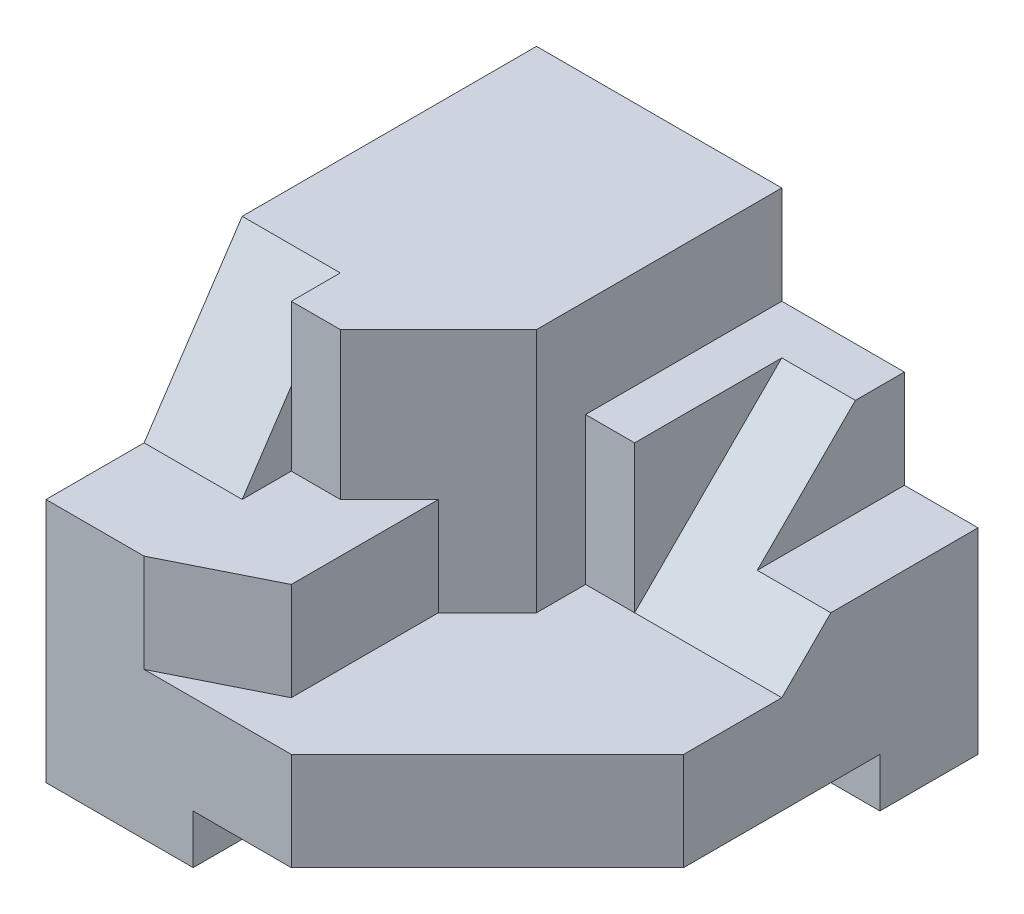
SolidWorks part; units mm, degrees
ref_plane "Front Plane" through (0, 0, 0) normal (0, 0, 1) x (1, 0, 0)
ref_plane "Top Plane" through (0, 0, 0) normal (0, 1, 0) x (1, 0, 0)
ref_plane "Right Plane" through (0, 0, 0) normal (1, 0, 0) x (0, 0, -1)
sketch "Sketch1" plane through (0, 0, 0) normal (0, 0, 1) x (1, 0, 0)
  line L1 (4.5, -4) -> (-4.5, -4)
  line L2 (4.5, -4) -> (4.5, 4)
  line L3 (4.5, 4) -> (-4.5, 4)
  line L4 (-4.5, -4) -> (-4.5, 4)
  line L5 (4.5, -4) -> (-4.5, 4) construction
  line L6 (4.5, 4) -> (-4.5, -4) construction
  point P0 (0, 0)
  dimension "D1" = 9
  dimension "D2" = 8
extrude "Boss-Extrude1" add sketch "Sketch1" along normal blind 10
sketch "Sketch3" plane through (4.5, 0, 0) normal (1, 0, 0) x (0, 0, -1)
  line L0 (0, 4) -> (0, 0)
  line L1 (0, -4) -> (0, 4) construction
  line L2 (0, 0) -> (-3, 0)
  line L3 (-3, 0) -> (-4, -1)
  line L4 (-4, -1) -> (-4, 4)
  line L5 (-10, 4) -> (0, 4) construction
  line L6 (-4, 4) -> (0, 4)
  dimension "D1" = 4
  dimension "D2" = 3
  dimension "D3" = 4
  dimension "D4" = 5
extrude "Cut-Extrude1" cut sketch "Sketch3" against normal blind 1.5
sketch "Sketch4" plane through (3, 0, 0) normal (1, 0, 0) x (0, 0, -1)
  line L0 (0, 4) -> (0, 2)
  line L1 (0, 0) -> (0, 4) construction
  line L2 (0, 2) -> (-1, 2)
  line L3 (-1, 2) -> (-4, -1)
  line L4 (-4, -1) -> (-4, 4)
  line L5 (-4, 4) -> (0, 4)
  line L6 (-4, -1) -> (-3, 0) construction
  dimension "D1" = 2
extrude "Cut-Extrude2" cut sketch "Sketch4" against normal blind 1.5
sketch "Sketch6" plane through (0, -4, 0) normal (0, -1, 0) x (1, 0, 0)
  line L0 (4.5, 2) -> (-1.5, 2)
  line L1 (4.5, 10) -> (4.5, 0) construction
  line L2 (-1.5, 2) -> (-1.5, 10)
  line L3 (-4.5, 10) -> (4.5, 10) construction
  line L4 (-1.5, 10) -> (4.5, 10)
  line L5 (4.5, 10) -> (4.5, 2)
  dimension "D1" = 2
  dimension "D2" = 3
extrude "Cut-Extrude3" cut sketch "Sketch6" against normal blind 1
sketch "Sketch7" plane through (0, -3, 0) normal (0, -1, 0) x (-1, 0, 0)
  line L0 (-4.5, -6) -> (-0.5, -10)
  line L1 (-4.5, -2) -> (-4.5, -10) construction
  line L2 (-4.5, -10) -> (1.5, -10) construction
  line L3 (-0.5, -10) -> (-4.5, -10)
  line L4 (-4.5, -10) -> (-4.5, -6)
  line L5 (-4.5, -6) -> (-4.4832, -5.9867)
  line M1 (-4.5, -2) -> (-4.5, -10)
  line M2 (-4.5, -10) -> (1.5, -10)
  dimension "D1" = 4
  dimension "D2" = 2
extrude "Cut-Extrude4" cut sketch "Sketch7" against normal through all contours L0 M1 M2
sketch "Sketch8" plane through (0, 4, 0) normal (0, 1, 0) x (1, 0, 0)
  line L0 (4.5, -4) -> (4.5, -6)
  line L1 (4.5, -6) -> (0.5, -10)
  line L2 (-0.5, -9) -> (-2.5, -10)
  line L4 (0.5, -10) -> (-4.5, -10) construction
  line L5 (-0.5, -9) -> (-0.5, -6)
  line L6 (-0.5, -6) -> (0.5, -5)
  line L7 (0.5, -5) -> (0.5, -4)
  line L8 (0.5, -4) -> (1.5, -4)
  line L9 (-2.5, -10) -> (0.5, -10)
  line L10 (1.5, -4) -> (4.5, -4)
  dimension "D1" = 3
  dimension "D2" = 3
  dimension "D3" = 1
  dimension "D4" = 1
  dimension "D5" = 2
  dimension "D6" = 1
extrude "Cut-Extrude5" cut sketch "Sketch8" against normal blind 5
sketch "Sketch9" plane through (1.5, 0, 0) normal (1, 0, 0) x (0, 0, -1)
  line L0 (-1, 2) -> (-4, 2)
  line L1 (-4, 4) -> (-4, -1) construction
  line L2 (-4, 2) -> (-4, 4)
  line L3 (-4, 4) -> (0, 4)
  line L4 (0, 4) -> (0, 2)
  line L5 (0, 2) -> (-1, 2)
extrude "Cut-Extrude6" cut sketch "Sketch9" against normal blind 1
sketch "Sketch10" plane through (-4.5, 0, 0) normal (-1, 0, 0) x (0, 0, 1)
  line L0 (6, 4) -> (8, 1)
  line L1 (10, 4) -> (0, 4) construction
  line L2 (8, 1) -> (10, 1)
  line L3 (10, 4) -> (10, -4) construction
  line L4 (10, 1) -> (10, 4)
  line L5 (10, 4) -> (6, 4)
  dimension "D1" = 2
  dimension "D2" = 6
  dimension "D3" = 3
extrude "Cut-Extrude9" cut sketch "Sketch10" against normal blind 2
sketch "Sketch12" plane through (0, 4, 0) normal (0, 1, 0) x (1, 0, 0)
  line L0 (0.5, -5) -> (-1.5, -7)
  line L1 (-1.5, -7) -> (-2.5, -7)
  line L2 (-2.5, -6) -> (-2.5, -8) construction
  line L3 (-2.5, -7) -> (-2.5, -10)
  line L4 (-2.5, -10) -> (0.5, -8.5)
  line L5 (0.5, -8.5) -> (0.5, -5)
  line L6 (0.5, -5) -> (-0.5, -6) construction
  line L7 (-0.5, -9) -> (-2.5, -10) construction
  dimension "D1" = 1
extrude "Cut-Extrude10" cut sketch "Sketch12" against normal blind 3
